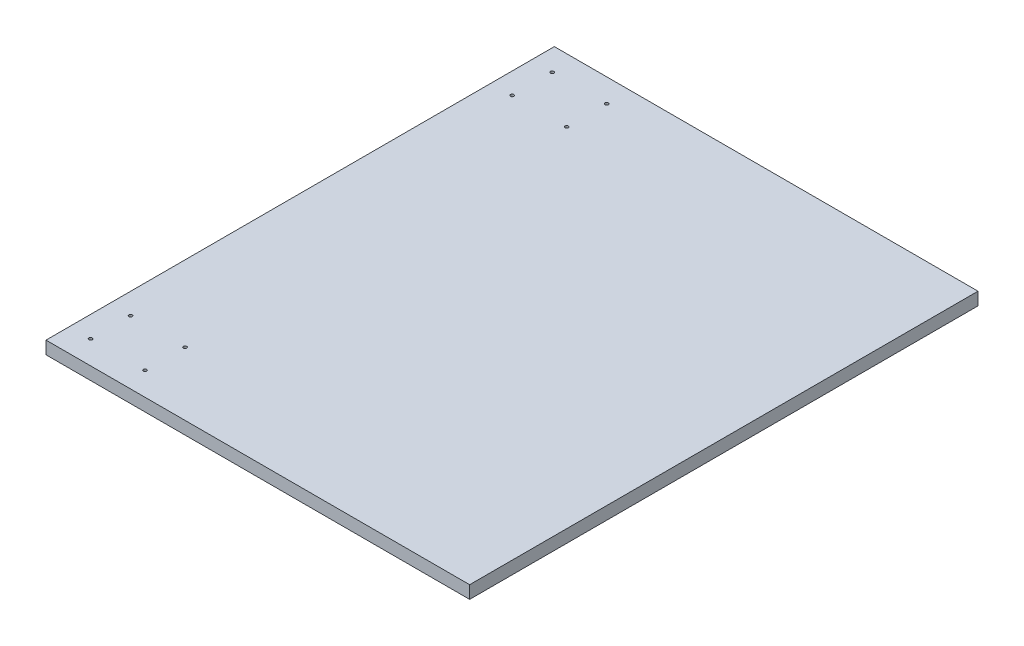
SolidWorks part; units mm, degrees
material "Cedar"
ref_plane "Front" through (0, 0, 0) normal (0, 0, 1) x (1, 0, 0)
ref_plane "Top" through (0, 0, 0) normal (0, 1, 0) x (1, 0, 0)
ref_plane "Right" through (0, 0, 0) normal (1, 0, 0) x (0, 0, -1)
sketch "Sketch1" plane through (0, 0, 0) normal (0, 1, 0) x (1, 0, 0)
  line L1 (-190.5, -228.6) -> (190.5, -228.6)
  line L2 (-190.5, -228.6) -> (-190.5, 228.6)
  line L3 (-190.5, 228.6) -> (190.5, 228.6)
  line L4 (190.5, -228.6) -> (190.5, 228.6)
  line L5 (-190.5, -228.6) -> (190.5, 228.6) construction
  line L6 (-190.5, 228.6) -> (190.5, -228.6) construction
  point P0 (0, 0)
  dimension "D1" = 457.2
  dimension "D2" = 381
extrude "Boss-Extrude1" add sketch "Sketch1" along normal blind 11.4554 contours L1 L4 L3 L2
sketch "Sketch3" plane through (0, 11.4554, 0) normal (0, 1, 0) x (1, 0, 0)
  line L1 (-171.45, 207.6) -> (-171.45, 171.6) construction
  line L2 (-171.45, 171.6) -> (-122.45, 171.6) construction
  line L3 (-122.45, 171.6) -> (-122.45, 207.6) construction
  line L4 (-122.45, 207.6) -> (-171.45, 207.6) construction
  line L5 (-190.5, 228.6) -> (190.5, 228.6) construction
  line L6 (-190.5, -228.6) -> (-190.5, 228.6) construction
  line L7 (130.8452, 0) -> (-366.2568, 0) construction
  circle A1 centre (-122.45, 207.6) radius 1.5
  circle A2 centre (-171.45, 207.6) radius 1.5
  circle A3 centre (-171.45, 171.6) radius 1.5
  circle A4 centre (-122.45, 171.6) radius 1.5
  circle A5 centre (-122.45, -171.6) radius 1.5
  circle A6 centre (-171.45, -171.6) radius 1.5
  circle A7 centre (-171.45, -207.6) radius 1.5
  circle A8 centre (-122.45, -207.6) radius 1.5
  dimension "D3" = 3
  dimension "D4" = 36
  dimension "D5" = 49
  dimension "D6" = 21
  dimension "D7" = 19.05
extrude "Cut-Extrude1" cut sketch "Sketch3" against normal through all
